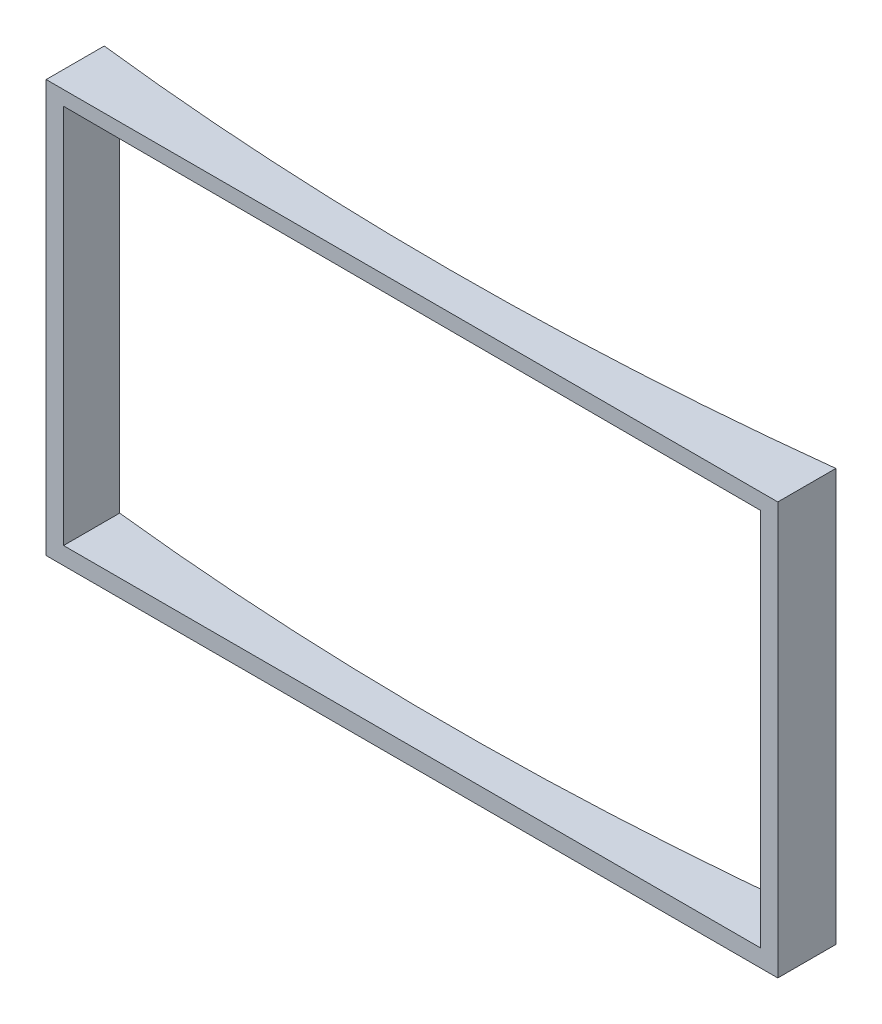
SolidWorks part; units mm, degrees
ref_plane "Front Plane" through (0, 0, 0) normal (0, 0, 1) x (1, 0, 0)
ref_plane "Top Plane" through (0, 0, 0) normal (0, 1, 0) x (1, 0, 0)
ref_plane "Right Plane" through (0, 0, 0) normal (1, 0, 0) x (0, 0, -1)
sketch "Sketch2" plane through (0, 0, 0) normal (0, 1, 0) x (1, 0, 0)
  line L0 (2590.5465, -3013.6099) -> (8890.5465, -3013.6099)
  line L1 (2590.5465, -3013.6099) -> (2590.5465, -2513.6099)
  line L2 (8890.5465, -3013.6099) -> (8890.5465, -2513.6099)
  arc A0 (2590.5465, -2513.6099) -> (8890.5465, -2513.6099) centre (5740.5465, 24805.3854) ccw
  point P3 (5740.5465, -3013.6099)
  dimension "D3" = 27500
  dimension "D1" = 6300
  dimension "D2" = 500
extrude "Boss-Extrude1" add sketch "Sketch2" along normal blind 3550
sketch "Sketch3" plane through (0, 0, 3013.6099) normal (0, 0, 1) x (1, 0, 0)
  line L0 (2590.5465, 3550) -> (2590.5465, 0) construction
  line L3 (2740.5465, 3425.6179) -> (8740.5465, 3412.6386)
  line L4 (8740.5465, 3412.6386) -> (8740.5465, 150)
  line L5 (8740.5465, 150) -> (2740.5465, 150)
  line L6 (2740.5465, 150) -> (2740.5465, 3425.6179)
  point P9 (5740.5465, 3419.1282)
  dimension "D1" = 150
  dimension "D2" = 6000
  dimension "D3" = 6000
extrude "Cut-Extrude1" cut sketch "Sketch3" against normal blind 6000
